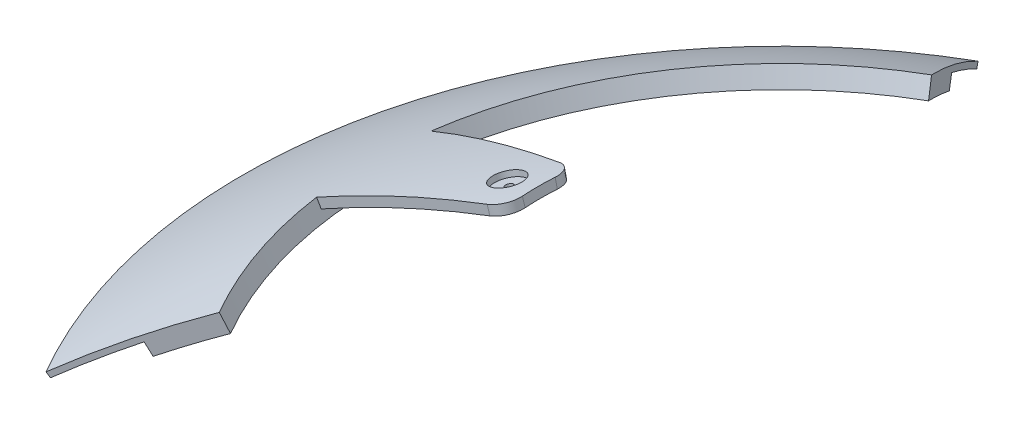
SolidWorks part; units mm, degrees
ref_plane "Front" through (0, 0, 0) normal (0, 0, 1) x (1, 0, 0)
ref_plane "Top" through (0, 0, 0) normal (0, 1, 0) x (1, 0, 0)
ref_plane "Right" through (0, 0, 0) normal (1, 0, 0) x (0, 0, -1)
sketch "Sketch2" plane through (0, 0, 0) normal (0, 0, 1) x (1, 0, 0)
  line L0 (0, 0) -> (-132.2383, 229.0435)
  line L1 (0, 0) -> (0, 226.0688)
  line L2 (0, 0) -> (-152.9275, 218.4031)
  line L3 (0, 0) -> (-117.2236, 240.344)
  circle A0 centre (0, 0) radius 250
  circle A1 centre (0, 0) radius 245
  circle A2 centre (0, 0) radius 248.5
  dimension "D1" = 500
  dimension "D2" = 490
  dimension "D5" = 497
  dimension "D3" = 30
  dimension "D4" = 5
  dimension "D6" = 26
revolve "Revolve1" add sketch "Sketch2" angle 30 about L1
sketch "Sketch3" plane through (0, 0, 0) normal (0, 0, 1) x (1, 0, 0)
  line L0 (0, 0) -> (0, 293.6545)
  line L1 (0, 0) -> (-67.1278, 250.5244)
  line L2 (0, 0) -> (-109.5928, 224.6985)
  line L3 (-109.5928, 224.6985) -> (-54.7964, 224.6985) construction
  circle A0 centre (0, 0) radius 250
  circle A1 centre (0, 0) radius 247.5
  dimension "D1" = 495
  dimension "D2" = 15
revolve "Revolve2" add sketch "Sketch3" angle 8 about L0 other way angle 8
fillet "Fillet1" radius 5 2 edges at (-63.7547, 240.274, -8.9601) (-63.7547, 240.274, 8.9601)
sketch "Sketch4" plane through (0, 0, 0) normal (0, 0, 1) x (1, 0, 0)
  line L0 (0, 0) -> (-75.8178, 248.5354)
  line L1 (0, 0) -> (-64.5449, 241.4785)
  line L2 (0.9569, 0.2905) -> (-76.0867, 252.8438)
  line L3 (3.8259, 1.1674) -> (-72.9725, 252.917)
  line L4 (-72.5083, 237.6864) -> (-68.6823, 238.8535)
  line L5 (0, 0) -> (0, 240.4253)
  line L6 (3.8259, 1.1671) -> (-62.6373, 219.0375) construction
  line L7 (0.9565, 0.2918) -> (-65.5067, 218.1621) construction
  line L8 (0, 0) -> (-66.4632, 217.8703) construction
  line L9 (-79.5453, 243.9009) -> (-64.5449, 250.7019)
  circle A0 centre (0, 0) radius 200
  dimension "D1" = 2
  dimension "D4" = 248.5
  dimension "D2" = 1
  dimension "D3" = 3
revolve "Cut-Revolve1" cut sketch "Sketch4" angle 360 about L0
sketch "Sketch7" plane through (0, 0, 0) normal (0, 0, 1) x (1, 0, 0)
  line L0 (0, 0) -> (0, 345.5294)
  line L1 (0, 0) -> (-169.7835, 261.5435)
  line L2 (0, 0) -> (-165.801, 270.5626)
  line L3 (0, 0) -> (-164.9726, 258.9551)
  circle A0 centre (0, 0) radius 248.5
  circle A1 centre (0, 0) radius 247
  circle A2 centre (0, 0) radius 245
  dimension "D1" = 497
  dimension "D2" = 494
  dimension "D3" = 490
  dimension "D4" = 32.99
  dimension "D5" = 0.49
  dimension "D6" = 1.49
revolve "Revolve3" add sketch "Sketch7" angle 7.5 about L0
